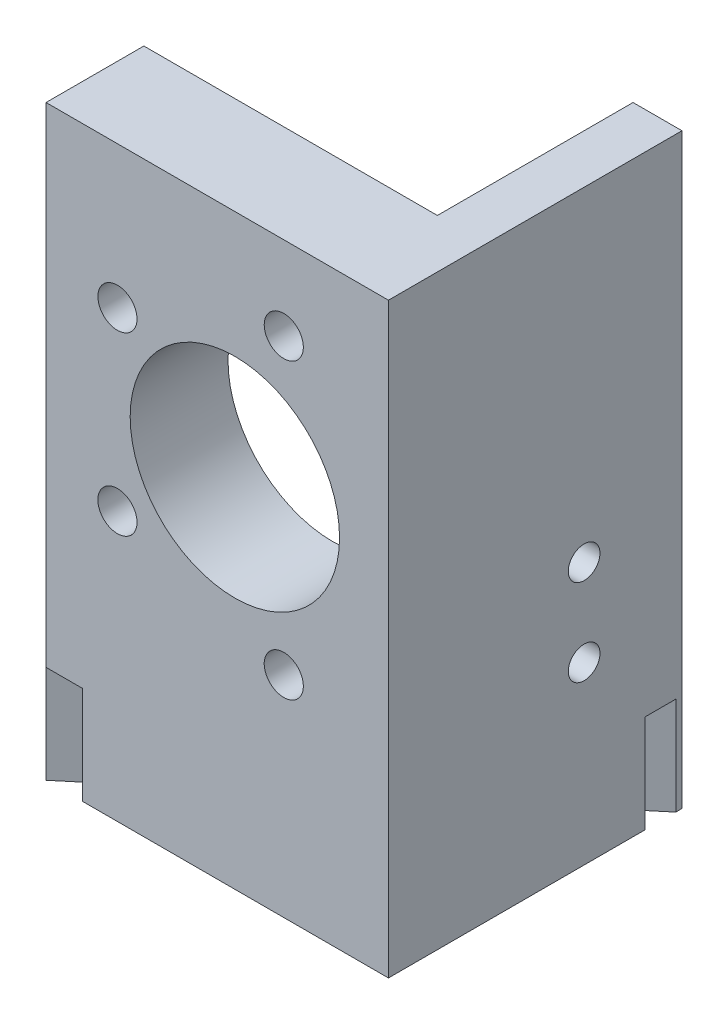
SolidWorks part; units mm, degrees
material "6061 Alloy"
ref_plane "Front Plane" through (0, 0, 0) normal (0, 0, 1) x (1, 0, 0)
ref_plane "Top Plane" through (0, 0, 0) normal (0, 1, 0) x (1, 0, 0)
ref_plane "Right Plane" through (0, 0, 0) normal (1, 0, 0) x (0, 0, -1)
sketch "Sketch1" plane through (0, 0, 0) normal (0, 1, 0) x (1, 0, 0)
  line L0 (-44.45, 12.7) -> (-44.45, 0)
  line L1 (-44.45, 0) -> (0, 0)
  line L2 (0, 0) -> (0, 38.1)
  line L3 (0, 38.1) -> (-6.35, 38.1)
  line L4 (-6.35, 38.1) -> (-6.35, 12.7)
  line L5 (-6.35, 12.7) -> (-44.45, 12.7)
  dimension "D1" = 12.7
  dimension "D2" = 38.1
  dimension "D3" = 6.35
  dimension "D4" = 25.4
extrude "Boss-Extrude1" add sketch "Sketch1" along normal blind 76.2
sketch "Sketch4" plane through (-6.35, 0, 0) normal (-1, 0, 0) x (0, 0, 1)
  line L0 (-25.4, 0) -> (-25.4, 76.2) construction
  line L1 (-38.1, 0) -> (-12.7, 0) construction
  line L2 (-38.1, 76.2) -> (-12.7, 76.2) construction
  circle A0 centre (-25.4, 22.7838) radius 2.0574
  circle A1 centre (-25.4, 34.036) radius 2.0574
  dimension "D1" = 11.2522
  dimension "D2" = 4.1148
  dimension "D3" = 34.036
extrude "Cut-Extrude3" cut sketch "Sketch4" against normal through all
sketch "Sketch3" plane through (0, 0, -12.7) normal (0, 0, -1) x (-1, 0, 0)
  line L0 (0, 76.2) -> (0, 0) construction
  line L1 (44.45, 46.3296) -> (19.939, 46.3296) construction
  line L2 (19.939, 46.3296) -> (-49980.061, 46.3296) construction
  line L3 (6.35, 31.9786) -> (6.35, 36.0934) construction
  line L4 (6.35, 31.9786) -> (6.35, 36.0934) construction
  line L5 (44.45, 76.2) -> (44.45, 0) construction
  line L6 (6.35, 76.2) -> (6.35, 0) construction
  circle A0 centre (19.939, 46.3296) radius 13.589
  circle A1 centre (35.179, 57.7596) radius 2.54
  circle A2 centre (13.589, 65.3796) radius 2.54
  circle A3 centre (13.589, 27.2796) radius 2.54
  circle A4 centre (35.179, 34.8996) radius 2.54
  point P4 (6.35, 34.036)
  point P21 (19.939, 46.3296)
  dimension "D1" = 15.24
  dimension "D5" = 5.08
  dimension "D2" = 12.2936
  dimension "D3" = 19.939
  dimension "D4" = 11.43
  dimension "D6" = 6.35
  dimension "D7" = 19.05
extrude "Cut-Extrude2" cut sketch "Sketch3" against normal through all
sketch "Sketch6" plane through (0, 0, 0) normal (0, -1, 0) x (1, 0, 0)
  line L0 (-47.8911, 6.8663) -> (10.4815, -42.1141)
  line L1 (10.4815, -42.1141) -> (8.5223, -44.449)
  line L2 (8.5223, -44.449) -> (-49.8503, 4.5314)
  line L3 (-49.8503, 4.5314) -> (-47.8911, 6.8663)
  line L4 (-44.45, 0) -> (0, 0) construction
  dimension "D1" = 3.048
  dimension "D2" = 40
  dimension "D3" = 76.2
extrude "Cut-Extrude4" cut sketch "Sketch6" against normal blind 12.7
sketch "Sketch7" plane through (-16.4065, 0, -19.5524) normal (-0.6428, 0, -0.766) x (-0.766, 0, 0.6428)
  line L0 (-24.4902, 25.7013) -> (34.0507, 25.7013) construction
  line L1 (-24.4902, 76.2) -> (-24.4902, 0) construction
  line L2 (34.0507, 76.2) -> (34.0507, 12.7) construction
  line L3 (4.7802, 76.2) -> (4.7802, 25.7013) construction
  line L4 (-3.299, 76.2) -> (25.8873, 76.2) construction
  line L5 (4.7802, 25.7013) -> (4.7802, 0) construction
  line L6 (-3.299, 0) -> (10.6605, 0) construction
  point P7 (4.7802, 25.7013)
ref_plane "Plane1" through (-21.3045, 0, -25.3897) normal (-0.6428, 0, -0.766) x (-0.766, 0, 0.6428)
sketch "Sketch9" plane through (-21.3045, 0, -25.3897) normal (-0.6428, 0, -0.766) x (-0.766, 0, 0.6428)
  line L0 (4.7802, 76.2) -> (4.7802, 25.7013) construction
  line L1 (4.7802, 25.7013) -> (4.7802, 0) construction
  line L2 (4.7802, 76.2) -> (4.7802, 25.7013) construction
  line L3 (4.7802, 25.7013) -> (4.7802, 0) construction
ref_plane "Center plane" through (-3.6619, 0, 3.0727) normal (-0.766, 0, 0.6428) x (0.6428, 0, 0.766)
